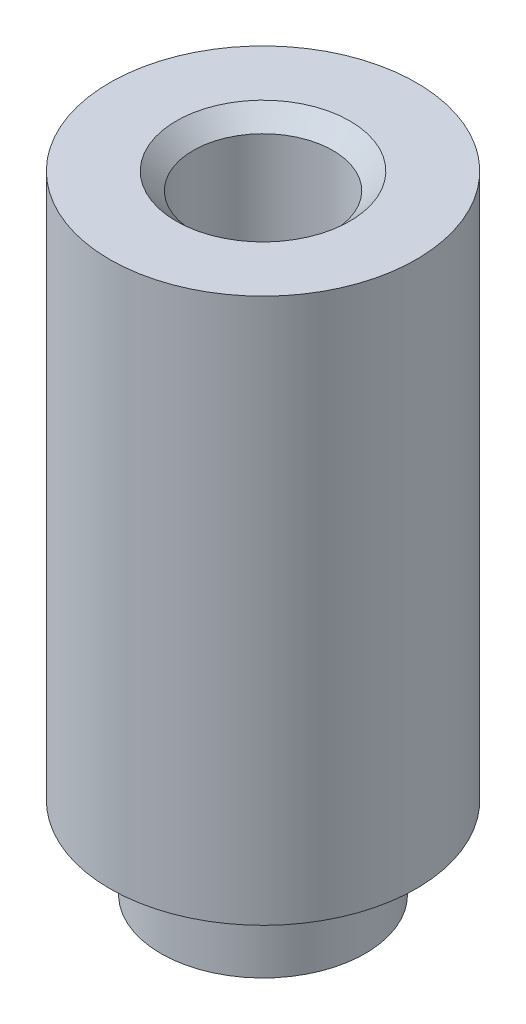
SolidWorks part; units mm, degrees
ref_plane "前视基准面" through (0, 0, 0) normal (0, 0, 1) x (1, 0, 0)
ref_plane "上视基准面" through (0, 0, 0) normal (0, 1, 0) x (1, 0, 0)
ref_plane "右视基准面" through (0, 0, 0) normal (1, 0, 0) x (0, 0, -1)
other "Configuration Table"
sketch "草图1" plane through (0, 0, 0) normal (0, 1, 0) x (1, 0, 0)
  circle A0 centre (0, 0) radius 1.5
  dimension "D1" = 3
extrude "凸台-拉伸1" add sketch "草图1" along normal blind 1.2
sketch "草图2" plane through (0, 1.2, 0) normal (0, 1, 0) x (1, 0, 0)
  circle A0 centre (0, 0) radius 2.25
  dimension "D1" = 4.5
extrude "凸台-拉伸2" add sketch "草图2" along normal blind 8
sketch "草图3" plane through (0, 9.2, 0) normal (0, 1, 0) x (1, 0, 0)
  point P0 (0, 0)
hole_wizard "M2.5 螺纹孔1" positions "草图4" profile "草图5" tap size "M2.5" standard "GB" end condition through all
sketch "草图4" plane through (0, 9.2, 0) normal (0, 1, 0) x (1, 0, 0)
  point P0 (0, 0)
sketch "草图5" plane through (0, 9.2, 0) normal (1, 0, 0) x (0, 0, 1)
  line L0 (0, 0) -> (0, 9.2)
  line L1 (0, 9.2) -> (1.025, 9.2)
  line L2 (1.025, 9.2) -> (1.025, 0.25)
  line L3 (1.025, 0.25) -> (1.275, 0)
  line L5 (1.275, 0) -> (0, 0)
  line L6 (-1.025, 0.25) -> (-1.275, 0) construction
  line L11 (0, -6.35) -> (0, 107.95) construction
  dimension "通孔螺纹孔钻头直径" = 2.05
  dimension "通孔螺纹孔钻头深度" = 9.2
  dimension "近端锥形沉头孔直径" = 2.55
  dimension "近端锥形沉头孔角度" = 90
cosmetic thread "孔螺蚊线1"
